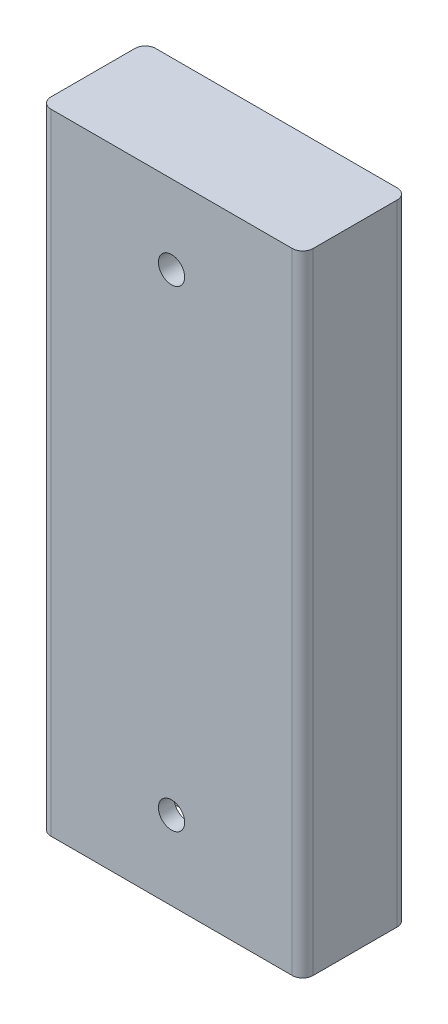
SolidWorks part; units mm, degrees
ref_plane "Front Plane" through (0, 0, 0) normal (0, 0, 1) x (1, 0, 0)
ref_plane "Top Plane" through (0, 0, 0) normal (0, 1, 0) x (1, 0, 0)
ref_plane "Right Plane" through (0, 0, 0) normal (1, 0, 0) x (0, 0, -1)
sketch "Sketch1" plane through (0, 0, 0) normal (0, 1, 0) x (1, 0, 0)
  line L1 (2, 0) -> (48, 0)
  line L2 (0, 2) -> (0, 18)
  line L3 (2, 20) -> (48, 20)
  line L4 (50, 2) -> (50, 18)
  arc A0 (2, 0) -> (0, 2) centre (2, 2) cw
  arc A1 (48, 0) -> (50, 2) centre (48, 2) ccw
  arc A2 (48, 20) -> (50, 18) centre (48, 18) cw
  arc A3 (0, 18) -> (2, 20) centre (2, 18) cw
  point P7 (0, 0)
  point P12 (50, 20)
  point P15 (0, 20)
  dimension "D3" = 2
  dimension "D1" = 50
  dimension "D2" = 20
extrude "Boss-Extrude1" add sketch "Sketch1" along normal blind 120
sketch "Sketch3" plane through (0, 0, 0) normal (0, -1, 0) x (1, 0, 0)
  line L29 (47, -17) -> (47, -3)
  line L30 (3, -17) -> (47, -17)
  line L31 (3, -3) -> (3, -17)
  line L32 (47, -3) -> (3, -3)
  line L33 (47, -17) -> (47, -3)
  line L34 (3, -17) -> (47, -17)
  line L35 (3, -3) -> (3, -17)
  line L36 (47, -3) -> (3, -3)
  dimension "D1" = 3
extrude "Cut-Extrude2" cut sketch "Sketch3" against normal blind 30 contours L35 L34 L33 L36
sketch "Sketch6" plane through (0, 0, 0) normal (0, 0, 1) x (1, 0, 0)
  line L0 (50, 120) -> (50, 0) construction
  line L1 (2, 120) -> (48, 120) construction
  line L2 (2, 0) -> (48, 0) construction
  circle A0 centre (25, 105) radius 2.5
  circle A1 centre (25, 15) radius 2.5
  dimension "D1" = 25
  dimension "D3" = 15
  dimension "D2" = 15
extrude "Cut-Extrude3" cut sketch "Sketch6" against normal blind 30
